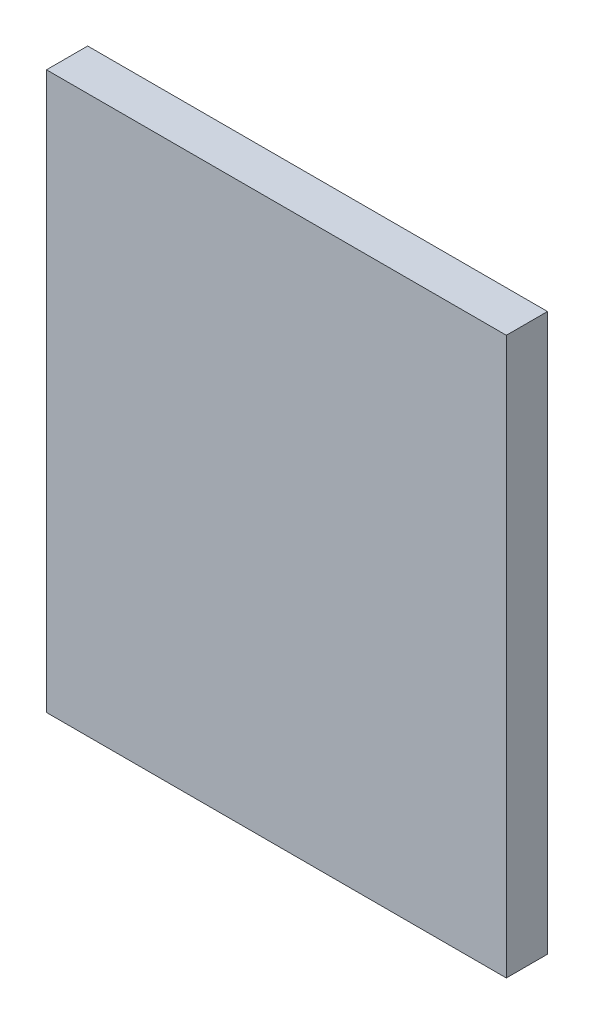
SolidWorks part; units mm, degrees
ref_plane "Front Plane" through (0, 0, 0) normal (0, 0, 1) x (1, 0, 0)
ref_plane "Top Plane" through (0, 0, 0) normal (0, 1, 0) x (1, 0, 0)
ref_plane "Right Plane" through (0, 0, 0) normal (1, 0, 0) x (0, 0, -1)
sketch "Sketch1" plane through (0, 0, 0) normal (0, 0, 1) x (1, 0, 0)
  line L1 (0, 0) -> (33.5, 0)
  line L2 (0, 0) -> (0, 40.55)
  line L3 (0, 40.55) -> (33.5, 40.55)
  line L4 (33.5, 0) -> (33.5, 40.55)
  dimension "D1" = 40.55
  dimension "D2" = 33.5
extrude "Boss-Extrude1" add sketch "Sketch1" along normal blind 3
